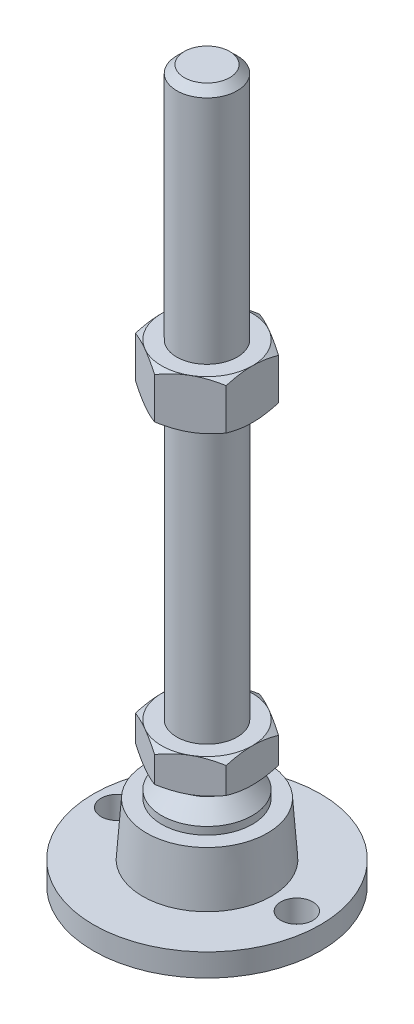
SolidWorks part; units mm, degrees
ref_plane "Спереди" through (0, 0, 0) normal (0, 0, 1) x (1, 0, 0)
ref_plane "Сверху" through (0, 0, 0) normal (0, 1, 0) x (1, 0, 0)
ref_plane "Справа" through (0, 0, 0) normal (1, 0, 0) x (0, 0, -1)
sketch "Эскиз1" plane through (0, 0, 0) normal (0, 0, 1) x (1, 0, 0)
  line L0 (0, 0) -> (-30, 0)
  line L3 (-30, 0) -> (-30, 6)
  line L12 (-8, 38) -> (-8, 186)
  line L13 (-8, 186) -> (-6, 188)
  line L14 (-6, 188) -> (0, 188)
  line L15 (0, 188) -> (0, 0) construction
  line L16 (-30, 6) -> (-17, 6)
  line L17 (0, 0) -> (0, 188)
  line L18 (0, 0) -> (0, -7.9595) construction
  line L19 (-8, 38) -> (-8, 29)
  line L21 (-12, 20) -> (-16, 20)
  line L22 (-17, 6) -> (-16, 20)
  line L23 (-12, 20) -> (-12, 22)
  line L24 (-12, 22) -> (-8, 26)
  line L25 (-8, 26) -> (-8, 29)
  line L26 (-8, 38) -> (0, 38) construction
  point P8 (-8, 112)
revolve "Повернуть1" add sketch "Эскиз1" angle 360 about L17
ref_plane "Плоскость2" through (0, 29, 0) normal (0, 1, 0) x (1, 0, 0)
sketch "Эскиз2" plane through (0, 29, 0) normal (0, 1, 0) x (1, 0, 0)
  line L1 (0, 13.8564) -> (-12, 6.9282)
  line L2 (-12, 6.9282) -> (-12, -6.9282)
  line L3 (-12, -6.9282) -> (0, -13.8564)
  line L4 (0, -13.8564) -> (12, -6.9282)
  line L5 (12, -6.9282) -> (12, 6.9282)
  line L6 (12, 6.9282) -> (0, 13.8564)
  circle A0 centre (0, 0) radius 12 construction
  dimension "D1" = 24
extrude "Бобышка-Вытянуть1" add sketch "Эскиз2" along normal up to vertex (9 mm away) up to point (-8, 38, 0)
ref_plane "Плоскость1" through (0, 112, 0) normal (0, 1, 0) x (1, 0, 0)
sketch "Эскиз3" plane through (0, 112, 0) normal (0, 1, 0) x (1, 0, 0)
  line L6 (12, 6.9282) -> (0, 13.8564)
  line L7 (0, 13.8564) -> (-12, 6.9282)
  line L8 (-12, 6.9282) -> (-12, -6.9282)
  line L9 (-12, -6.9282) -> (0, -13.8564)
  line L10 (0, -13.8564) -> (12, -6.9282)
  line L11 (12, -6.9282) -> (12, 6.9282)
  line L12 (12, 6.9282) -> (0, 13.8564)
  line L13 (0, 13.8564) -> (-12, 6.9282)
  line L14 (-12, 6.9282) -> (-12, -6.9282)
  line L15 (-12, -6.9282) -> (0, -13.8564)
  line L16 (0, -13.8564) -> (12, -6.9282)
  line L17 (12, -6.9282) -> (12, 6.9282)
  dimension "D1" = 0
extrude "Бобышка-Вытянуть2" add sketch "Эскиз3" along normal blind 13
sketch "Эскиз4" plane through (0, 0, 0) normal (0, 0, 1) x (1, 0, 0)
  line L0 (-12, 125) -> (-23.2583, 118.5)
  line L1 (-23.2583, 118.5) -> (-23.2583, 125)
  line L2 (-23.2583, 125) -> (-12, 125)
  line L3 (-23.2583, 118.5) -> (-12, 112)
  line L4 (50, 112) -> (-50, 112) construction
  line L5 (-12, 112) -> (-23.2583, 112)
  line L6 (-23.2583, 112) -> (-23.2583, 118.5)
  line L7 (-12, 125) -> (-12, 112) construction
  line L8 (-12, 38) -> (-19.7942, 38)
  line L9 (-19.7942, 38) -> (-19.7942, 33.5)
  line L10 (-19.7942, 33.5) -> (-12, 38)
  line L11 (-12, 29) -> (-19.7942, 33.5)
  line L12 (-19.7942, 33.5) -> (-19.7942, 29)
  line L13 (-19.7942, 29) -> (-12, 29)
  line L14 (0, 188) -> (0, 96.3793) construction
  line L15 (50, 29) -> (-50, 29) construction
  dimension "D1" = 30
  dimension "D2" = 30
revolve "Вырез-Повернуть2" cut sketch "Эскиз4" angle 360 about L14
sketch "Эскиз5" plane through (0, 6, 0) normal (0, 1, 0) x (1, 0, 0)
  line L0 (23.75, 0) -> (-23.75, 0) construction
  circle A0 centre (-23.75, 0) radius 4.25
  circle A1 centre (23.75, 0) radius 4.25
  circle A2 centre (0, 0) radius 30 construction
  dimension "D1" = 8.5
  dimension "D2" = 2
extrude "Вырез-Вытянуть1" cut sketch "Эскиз5" against normal through all
equation "\"D13@Эскиз1\"=\"D12@Эскиз1\"/2"
